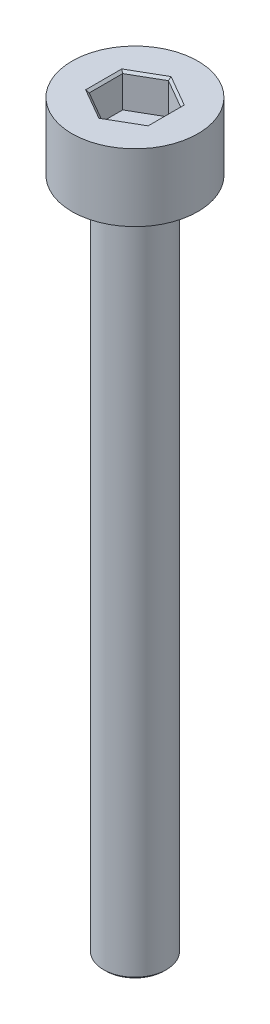
SolidWorks part; units mm, degrees
material "铸造合金钢"
ref_plane "前视基准面" through (0, 0, 0) normal (0, 0, 1) x (1, 0, 0)
ref_plane "上视基准面" through (0, 0, 0) normal (0, 1, 0) x (1, 0, 0)
ref_plane "右视基准面" through (0, 0, 0) normal (1, 0, 0) x (0, 0, -1)
sketch "草图1" plane through (0, 0, 0) normal (0, 1, 0) x (1, 0, 0)
  circle A0 centre (0, 0) radius 2.8
  dimension "D1" = 5.6
extrude "凸台-拉伸1" add sketch "草图1" along normal blind 3
sketch "草图2" plane through (0, 3, 0) normal (0, 1, 0) x (1, 0, 0)
  line L1 (0, -1.4896) -> (1.29, -0.7448)
  line L2 (1.29, -0.7448) -> (1.29, 0.7448)
  line L3 (1.29, 0.7448) -> (0, 1.4896)
  line L4 (0, 1.4896) -> (-1.29, 0.7448)
  line L5 (-1.29, 0.7448) -> (-1.29, -0.7448)
  line L6 (-1.29, -0.7448) -> (0, -1.4896)
  circle A0 centre (0, 0) radius 1.29 construction
  dimension "D1" = 2.58
extrude "切除-拉伸1" cut sketch "草图2" against normal blind 1.5
sketch "草图3" plane through (0, 0, 0) normal (0, -1, 0) x (1, 0, 0)
  circle A0 centre (0, 0) radius 1.4
  dimension "D1" = 2.8
extrude "凸台-拉伸2" add sketch "草图3" along normal blind 30
chamfer "倒角1" distance 0.1 angle 45 7 edges at (0.645, 3, -1.1172) (-0.645, 3, -1.1172) (-1.29, 3, 0) (-0.645, 3, 1.1172) (0.645, 3, 1.1172) (1.29, 3, 0) (0, -30, -1.4)
